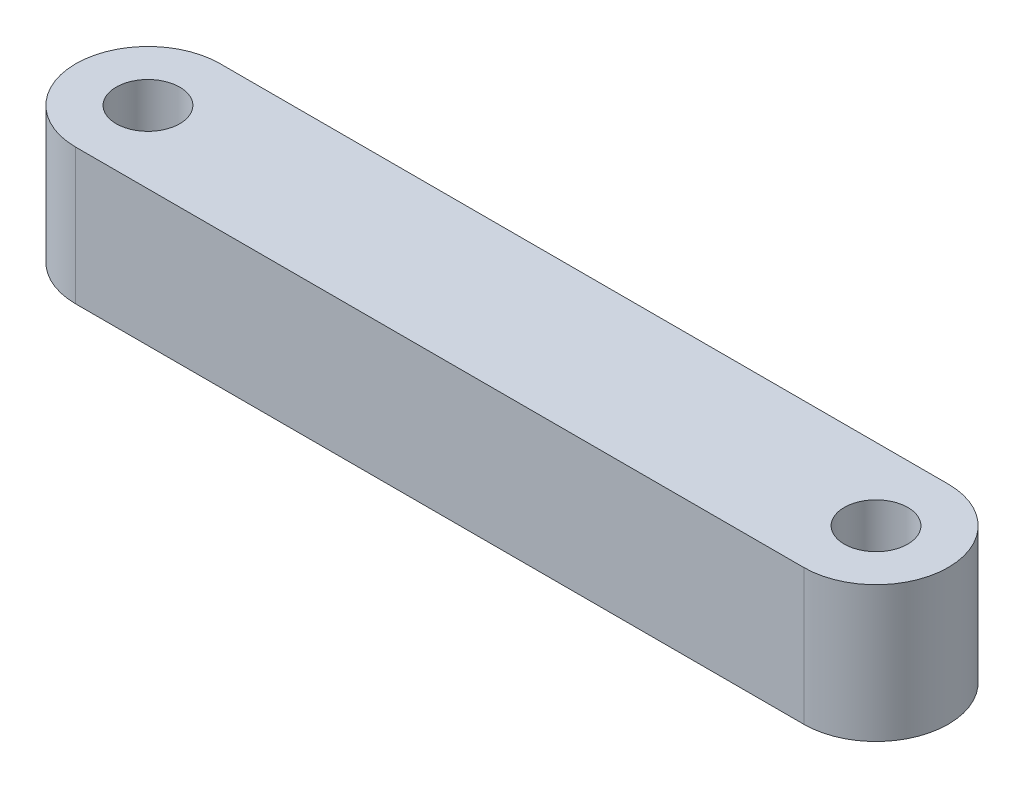
SolidWorks part; units mm, degrees
ref_plane "Front Plane" through (0, 0, 0) normal (0, 0, 1) x (1, 0, 0)
ref_plane "Top Plane" through (0, 0, 0) normal (0, 1, 0) x (1, 0, 0)
ref_plane "Right Plane" through (0, 0, 0) normal (1, 0, 0) x (0, 0, -1)
sketch "Sketch1" plane through (0, 0, 0) normal (0, 1, 0) x (1, 0, 0)
  line L0 (-16, 0) -> (16, 0) construction
  line L1 (-16, 0) -> (16, 0) construction
  line L2 (-16, 3.175) -> (16, 3.175)
  line L3 (-16, -3.175) -> (16, -3.175)
  circle A0 centre (-16, 0) radius 1.397
  circle A1 centre (16, 0) radius 1.397
  arc A2 (-16, 3.175) -> (-16, -3.175) centre (-16, 0) ccw
  arc A3 (16, -3.175) -> (16, 3.175) centre (16, 0) ccw
  point P6 (0, 0)
  dimension "D2" = 2.794
  dimension "D3" = 6.35
  dimension "D1" = 32
extrude "Boss-Extrude1" add sketch "Sketch1" along normal blind 5.969
